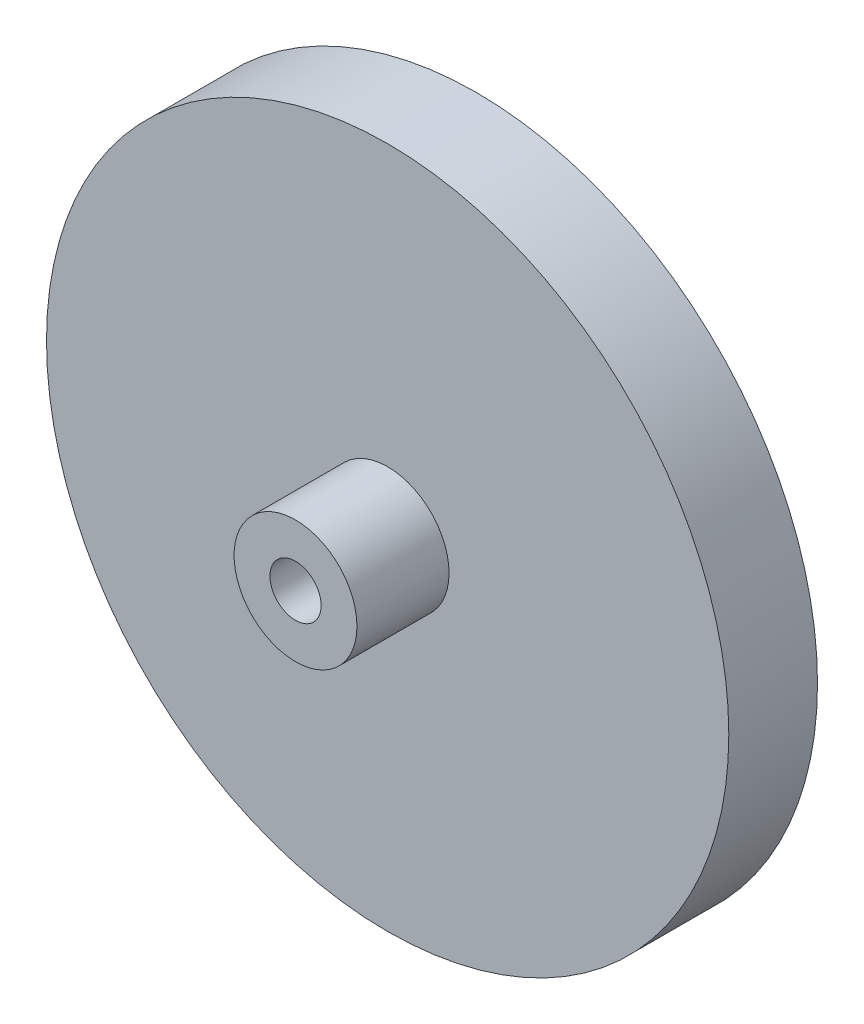
SolidWorks part; units mm, degrees
ref_plane "Front Plane" through (0, 0, 0) normal (0, 0, 1) x (1, 0, 0)
ref_plane "Top Plane" through (0, 0, 0) normal (0, 1, 0) x (1, 0, 0)
ref_plane "Right Plane" through (0, 0, 0) normal (1, 0, 0) x (0, 0, -1)
sketch "Sketch1" plane through (0, 0, 0) normal (0, 0, 1) x (1, 0, 0)
  circle A0 centre (0, 0) radius 25
  dimension "D1" = 50
extrude "Boss-Extrude2" add sketch "Sketch1" along normal mid plane 6.5
sketch "Sketch2" plane through (0, 0, 0) normal (0, 0, 1) x (1, 0, 0)
  circle A0 centre (0, 0) radius 4.5
  dimension "D1" = 9
extrude "Boss-Extrude3" add sketch "Sketch2" along normal blind 10
sketch "Sketch3" plane through (0, 0, -3.25) normal (0, 0, -1) x (-1, 0, 0)
  circle A0 centre (0, 0) radius 4.5
  dimension "D1" = 9
extrude "Boss-Extrude4" add sketch "Sketch3" along normal blind 5
sketch "Sketch4" plane through (0, 0, -8.25) normal (0, 0, -1) x (-1, 0, 0)
  circle A0 centre (0, 0) radius 3.1
  dimension "D1" = 6.2
extrude "Cut-Extrude1" cut sketch "Sketch4" against normal blind 2.5
sketch "Sketch6" plane through (0, 0, 10) normal (0, 0, 1) x (1, 0, 0)
  circle A0 centre (0, 0) radius 1.875
  dimension "D1" = 3.75
extrude "Cut-Extrude2" cut sketch "Sketch6" against normal through all both and the other way through all
